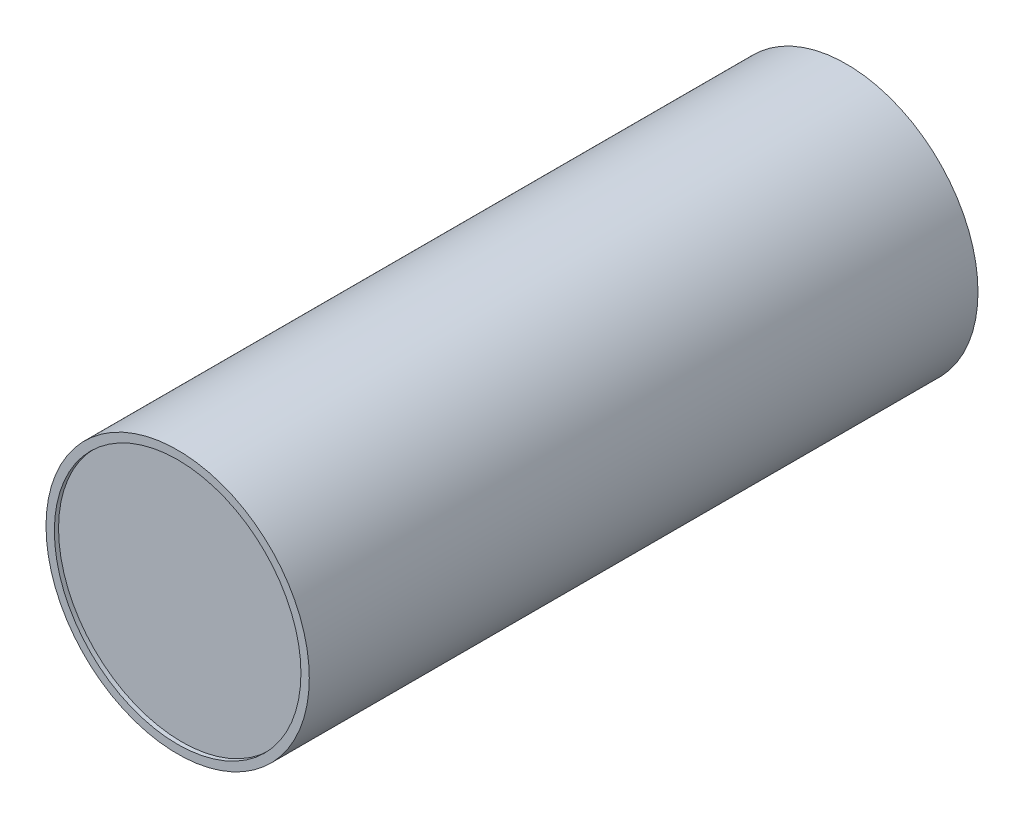
SolidWorks part; units mm, degrees
ref_plane "Plan de face" through (0, 0, 0) normal (0, 0, 1) x (1, 0, 0)
ref_plane "Plan de dessus" through (0, 0, 0) normal (0, 1, 0) x (1, 0, 0)
ref_plane "Plan de droite" through (0, 0, 0) normal (1, 0, 0) x (0, 0, -1)
sketch "Esquisse1" plane through (0, 0, 0) normal (0, 0, 1) x (1, 0, 0)
  circle A0 centre (0, 0) radius 31.5
  circle A1 centre (0, 0) radius 29.5
  dimension "D1" = 63
  dimension "D2" = 2
extrude "Boss.-Extru.1" add sketch "Esquisse1" along normal blind 160 contours A1
ref_plane "Plan1" through (0, 0, 1) normal (0, 0, -1) x (-1, 0, 0)
sketch "Esquisse2" plane through (0, 0, 1) normal (0, 0, -1) x (-1, 0, 0)
  circle A0 centre (0, 0) radius 30
  dimension "D1" = 60
extrude "Boss.-Extru.2" add sketch "Esquisse2" against normal blind 5
ref_plane "Plan2" through (0, 0, 159) normal (0, 0, 1) x (1, 0, 0)
sketch "Esquisse3" plane through (0, 0, 159) normal (0, 0, 1) x (1, 0, 0)
  circle A0 centre (0, 0) radius 30
  dimension "D1" = 60
extrude "Boss.-Extru.3" add sketch "Esquisse3" against normal blind 5
